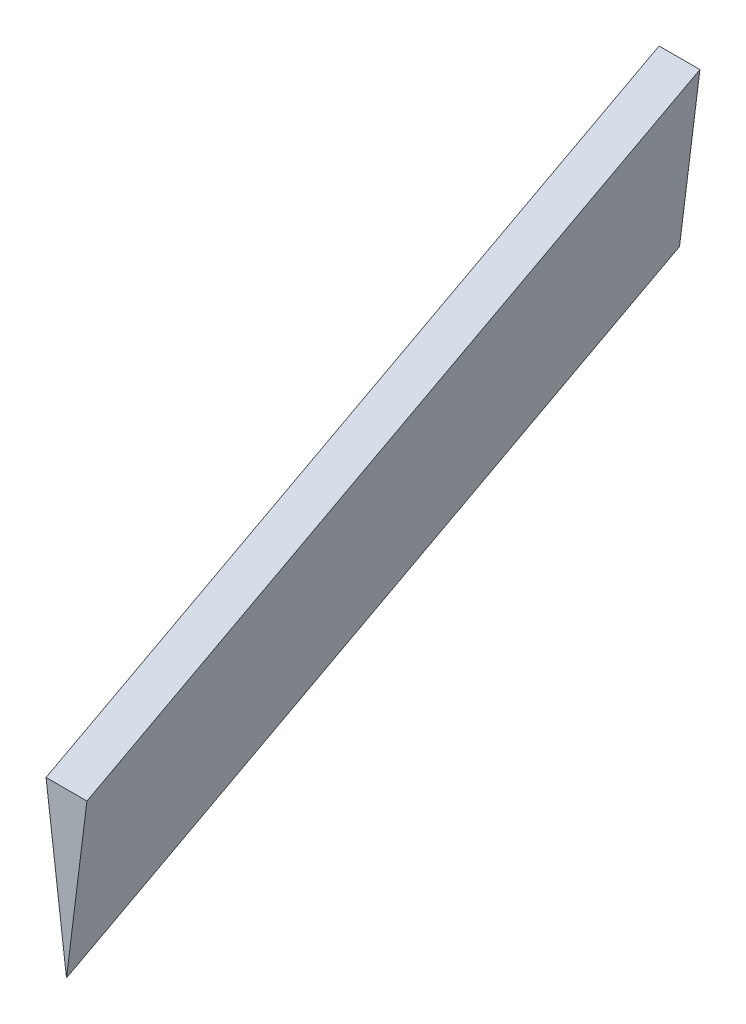
SolidWorks part; units mm, degrees
material "E-Glass Fiber"
ref_plane "Front Plane" through (0, 0, 0) normal (0, 0, 1) x (1, 0, 0)
ref_plane "Top Plane" through (0, 0, 0) normal (0, 1, 0) x (1, 0, 0)
ref_plane "Right Plane" through (0, 0, 0) normal (1, 0, 0) x (0, 0, -1)
sketch "Sketch1" plane through (0, 0, 0) normal (1, 0, 0) x (0, 0, -1)
  line L0 (0, 0) -> (95.25, 50.8)
  dimension "D1" = 95.25
  dimension "D2" = 50.8
sketch "Sketch2" plane through (0, 0, 0) normal (0, 0, 1) x (1, 0, 0)
  line L0 (-3.175, 0) -> (0, -25.4)
  line L1 (0, -25.4) -> (3.175, 0)
  line L2 (3.175, 0) -> (-3.175, 0)
  dimension "D1" = 6.35
  dimension "D2" = 25.4
sweep "Sweep1" add profiles "Sketch2" path "Sketch1"
